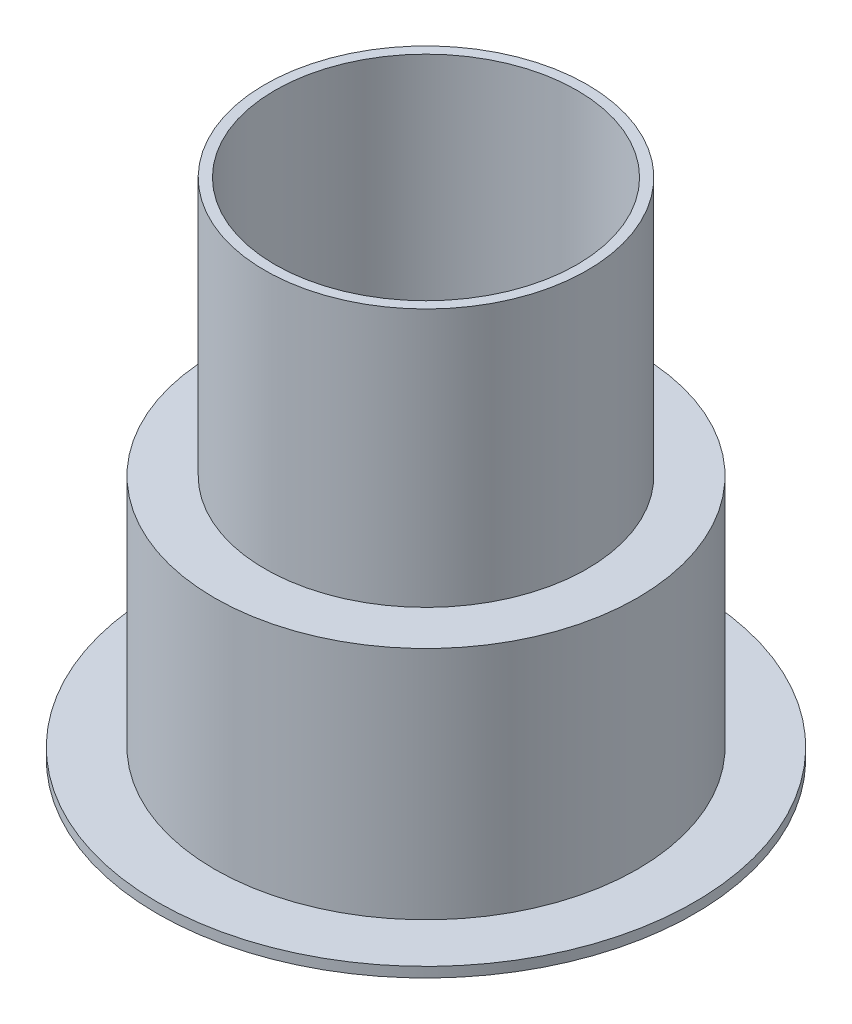
SolidWorks part; units mm, degrees
ref_plane "Front Plane" through (0, 0, 0) normal (0, 0, 1) x (1, 0, 0)
ref_plane "Top Plane" through (0, 0, 0) normal (0, 1, 0) x (1, 0, 0)
ref_plane "Right Plane" through (0, 0, 0) normal (1, 0, 0) x (0, 0, -1)
sketch "Sketch1" plane through (0, 0, 0) normal (0, 0, 1) x (1, 0, 0)
  line L0 (0, 0) -> (0, 13.5207) construction
  line L1 (6, -0.8548) -> (6, 6.1452)
  line L2 (6, 6.1452) -> (0, 6.1452)
  line L3 (4.5, 6.4452) -> (4.5, 14.1452)
  line L4 (6, -0.8548) -> (8, -0.8548)
  line L5 (4.8, 6.4452) -> (4.8, 14.1452)
  line L6 (6.3, -0.5548) -> (8, -0.5548)
  line L7 (6.3, -0.5548) -> (6.3, 6.4452)
  line L8 (6.3, 6.4452) -> (4.8, 6.4452)
  line L9 (0, 6.4452) -> (0, 6.1452)
  line L10 (4.5, 14.1452) -> (4.8, 14.1452)
  line L11 (8, -0.8548) -> (8, -0.5548)
  line L12 (4.5, 6.1452) -> (4.5, 14.1452) construction
  line L13 (4.5, 6.4452) -> (0, 6.4452)
  line L14 (6.3, 6.4452) -> (0, 6.4452) construction
  line L15 (4.8, 6.1452) -> (4.8, 14.1452) construction
  dimension "D1" = 6
  dimension "D2" = 2
  dimension "D3" = 7
  dimension "D5" = 1.5
  dimension "D6" = 0.3
  dimension "D7" = 0.3
revolve "Revolve1" add sketch "Sketch1" angle 360 about L0
